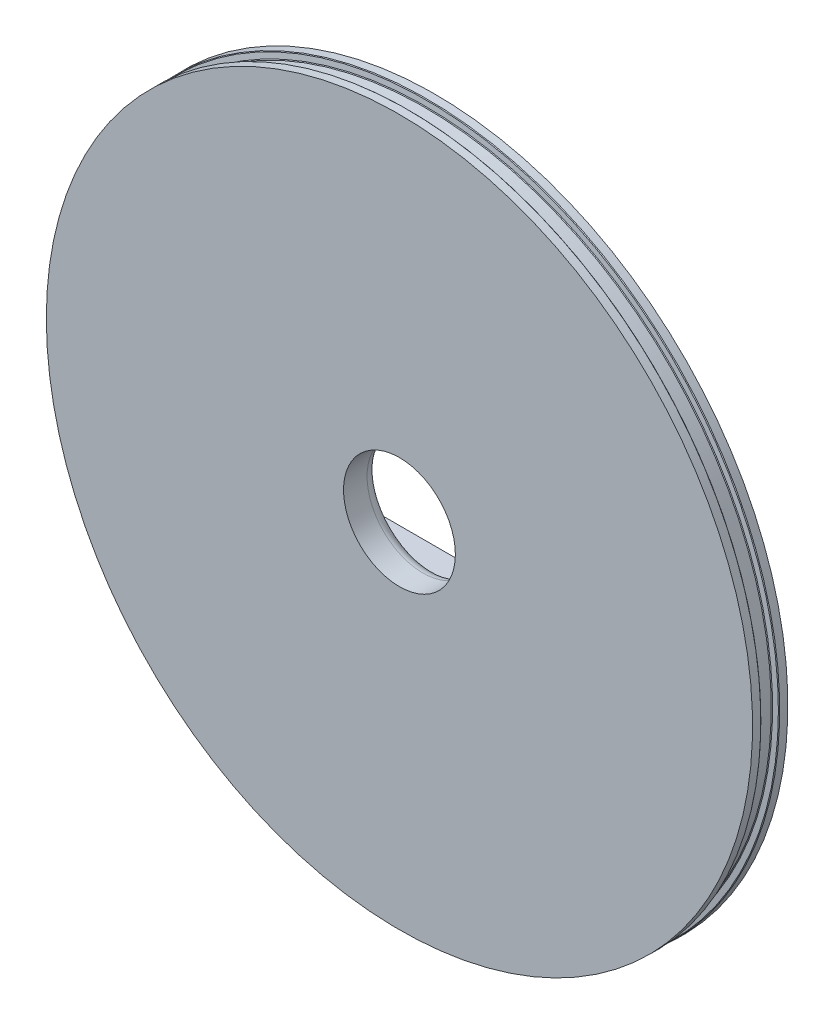
SolidWorks part; units mm, degrees
ref_plane "Front Plane" through (0, 0, 0) normal (0, 0, 1) x (1, 0, 0)
ref_plane "Top Plane" through (0, 0, 0) normal (0, 1, 0) x (1, 0, 0)
ref_plane "Right Plane" through (0, 0, 0) normal (1, 0, 0) x (0, 0, -1)
sketch "Sketch1" plane through (0, 0, 0) normal (0, 0, 1) x (1, 0, 0)
  circle A0 centre (0, 0) radius 76.2
  dimension "D1" = 152.4
extrude "Boss-Extrude1" add sketch "Sketch1" along normal blind 7.62
sketch "Sketch2" plane through (0, 0, 0) normal (1, 0, 0) x (0, 0, -1)
  line L0 (-1.9076, 76.2) -> (-2.032, 74.7776)
  line L1 (-5.588, 74.7776) -> (-5.588, 76.2) construction
  line L2 (-3.81, 76.2) -> (-3.81, 74.7776) construction
  line L3 (0, 76.2) -> (-7.62, 76.2) construction
  line L4 (-5.7124, 76.2) -> (-5.588, 74.7776)
  line L5 (-5.588, 74.7776) -> (-2.032, 74.7776)
  line L6 (-5.7124, 76.2) -> (-1.9076, 76.2)
  line L7 (0, 0) -> (-7.62, 0) construction
  line L8 (-7.62, 76.2) -> (-7.62, -76.2) construction
  dimension "OD" = 3.556
  dimension "Depth of Groove" = 1.4224
  dimension "D3" = 5
revolve "Cut-Revolve1" cut sketch "Sketch2" angle 360 about L7
chamfer "Chamfer1" distance 0.13 angle 45 4 edges at (-76.2, 0, 1.9076) (-74.7776, 0, 2.032) (-76.2, 0, 5.7124) (-74.7776, 0, 5.588)
sketch "Sketch3" plane through (0, 0, 7.62) normal (0, 0, 1) x (1, 0, 0)
  circle A0 centre (0, 0) radius 12.065
  dimension "D1" = 24.13
extrude "Cut-Extrude1" cut sketch "Sketch3" against normal up to surface (7.62 mm away) up to face at (76.2, 0, 0)
sketch "Sketch4" plane through (0, 0, 0) normal (0, 0, -1) x (-1, 0, 0)
  line L0 (-19.685, 19.685) -> (48.895, 19.685)
  line L1 (-15.875, 15.875) -> (45.085, 15.875)
  line L2 (-15.875, 15.875) -> (-15.875, -29.0859)
  line L3 (-15.875, -29.0859) -> (45.085, -29.0859)
  line L4 (45.085, 15.875) -> (45.085, -29.0859)
  line L5 (48.895, 19.685) -> (48.895, -32.8959)
  line L6 (-19.685, -32.8959) -> (48.895, -32.8959)
  line L7 (-19.685, 19.685) -> (-19.685, -32.8959)
  circle A0 centre (0, 0) radius 12.065 construction
  dimension "D1" = 3.81
  dimension "D2" = 3.81
  dimension "D3" = 60.96
  dimension "D4" = 44.9609
  dimension "D5" = 3.81
extrude "Boss-Extrude2" add sketch "Sketch4" along normal blind 20.828
sketch "Sketch5" plane through (0, 0, -20.828) normal (0, 0, -1) x (-1, 0, 0)
  line L0 (-19.685, 19.685) -> (-19.685, -32.8959) construction
  line L1 (-15.875, -29.0859) -> (-19.685, -29.0859)
  line L2 (-15.875, -29.0859) -> (-15.875, 10.795)
  line L3 (-15.875, 10.795) -> (-19.685, 10.795)
  line L4 (-19.685, -29.0859) -> (-19.685, 10.795)
  line L5 (48.895, 19.685) -> (-19.685, 19.685) construction
  dimension "D1" = 8.89
extrude "Cut-Extrude3" cut sketch "Sketch5" against normal up to surface (20.828 mm away) up to face at (76.2, 0, 0)
fillet "Fillet1" radius 2.54 14 edges at (12.065, 0, 0) (19.685, -30.9909, 0) (17.78, 10.795, 0) (-14.605, -32.8959, 0) (-14.605, 19.685, 0) (19.685, 19.685, -10.414) (19.685, 15.24, -20.828) (19.685, 10.795, -10.414) (19.685, 15.24, 0) (-48.895, -32.8959, -10.414) (-48.895, -6.6055, -20.828) (-48.895, 19.685, -10.414) (-48.895, -6.6055, 0) (19.685, -32.8959, -10.414)
equation "\"Depth of Groove@Sketch2\"=\"OD@Sketch2\"*.40"
